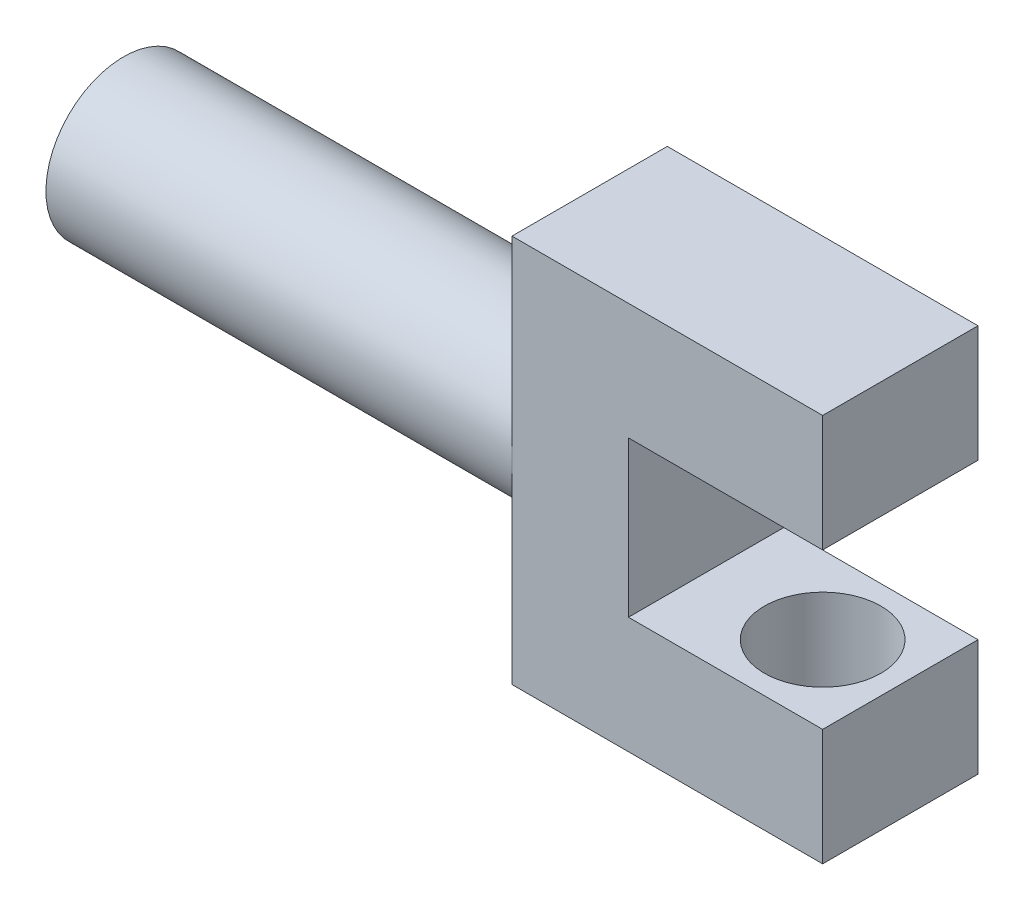
SolidWorks part; units mm, degrees
ref_plane "Front Plane" through (0, 0, 0) normal (0, 0, 1) x (1, 0, 0)
ref_plane "Top Plane" through (0, 0, 0) normal (0, 1, 0) x (1, 0, 0)
ref_plane "Right Plane" through (0, 0, 0) normal (1, 0, 0) x (0, 0, -1)
sketch "Sketch2" plane through (0, 0, 0) normal (0, 0, 1) x (1, 0, 0)
  line L0 (0, 25) -> (0, -25)
  line L1 (0, 25) -> (40, 25)
  line L2 (40, 25) -> (40, 10)
  line L3 (40, 10) -> (15, 10)
  line L4 (15, 10) -> (15, -10)
  line L5 (-45.7091, 0) -> (61.0391, 0) construction
  line L7 (40, -10) -> (15, -10)
  line L8 (40, -25) -> (40, -10)
  line L9 (0, -25) -> (40, -25)
  point P10 (15, 0)
  point P11 (0, 0)
  dimension "D1" = 25
  dimension "D2" = 40
  dimension "D3" = 25
  dimension "D4" = 10
extrude "Boss-Extrude1" add sketch "Sketch2" along normal mid plane 20
sketch "Sketch3" plane through (0, 0, 0) normal (-1, 0, 0) x (0, 0, 1)
  circle A0 centre (0, 0) radius 10
  dimension "D1" = 20
extrude "Boss-Extrude2" add sketch "Sketch3" along normal blind 60
sketch "Sketch4" plane through (0, 10, 0) normal (0, -1, 0) x (1, 0, 0)
  line L0 (0, 10) -> (0, -10) construction
  circle A0 centre (30, 0) radius 7.5
  dimension "D1" = 15
  dimension "D2" = 30
extrude "Cut-Extrude1" cut sketch "Sketch4" against normal blind 12 and the other way blind 32
